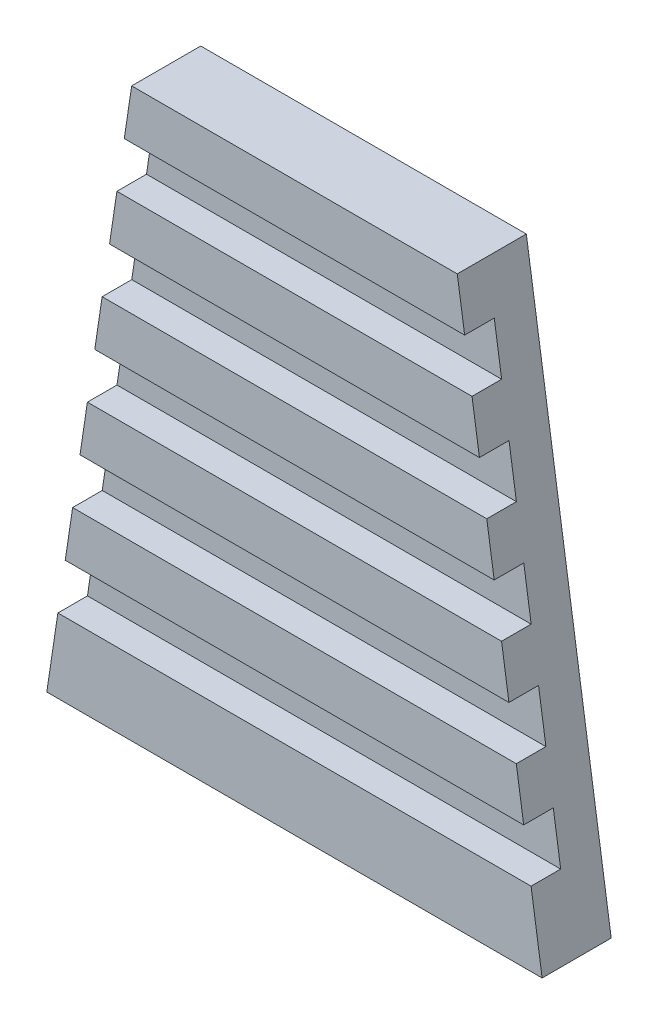
SolidWorks part; units mm, degrees
material "ABS"
ref_plane "Front Plane" through (0, 0, 0) normal (0, 0, 1) x (1, 0, 0)
ref_plane "Top Plane" through (0, 0, 0) normal (0, 1, 0) x (1, 0, 0)
ref_plane "Right Plane" through (0, 0, 0) normal (1, 0, 0) x (0, 0, -1)
sketch "Sketch1" plane through (0, 0, 0) normal (0, 0, 1) x (1, 0, 0)
  line L0 (-25.1, -28.75) -> (-16.5, 28.75)
  line L1 (-16.5, 28.75) -> (16.5, 28.75)
  line L2 (16.5, 28.75) -> (25.1, -28.75)
  line L3 (25.1, -28.75) -> (-25.1, -28.75)
  line L4 (0, -28.75) -> (0, 28.75) construction
  point P6 (0, 0)
  dimension "D1" = 57.5
  dimension "D2" = 33
  dimension "D3" = 50.2
extrude "Extrude1" add sketch "Sketch1" along normal blind 4
sketch "Sketch2" plane through (0, 0, 4) normal (0, 0, 1) x (1, 0, 0)
  line L4 (-17.2478, 23.75) -> (17.2478, 23.75)
  line L5 (-17.9957, 18.75) -> (17.9957, 18.75)
  line L6 (-18.7435, 13.75) -> (18.7435, 13.75)
  line L7 (-19.4913, 8.75) -> (19.4913, 8.75)
  line L8 (-25.1, -28.75) -> (25.1, -28.75)
  line L9 (25.1, -28.75) -> (16.5, 28.75)
  line L10 (16.5, 28.75) -> (-16.5, 28.75)
  line L11 (-16.5, 28.75) -> (-25.1, -28.75)
  line L12 (-25.1, -28.75) -> (25.1, -28.75)
  line L13 (25.1, -28.75) -> (23.9783, -21.25)
  line L14 (16.5, 28.75) -> (-16.5, 28.75)
  line L15 (-16.5, 28.75) -> (-17.2478, 23.75)
  line L16 (-20.2391, 3.75) -> (20.2391, 3.75)
  line L17 (-20.987, -1.25) -> (20.987, -1.25)
  line L18 (-21.7348, -6.25) -> (21.7348, -6.25)
  line L19 (-22.4826, -11.25) -> (22.4826, -11.25)
  line L20 (-23.2304, -16.25) -> (23.2304, -16.25)
  line L21 (-23.9783, -21.25) -> (23.9783, -21.25)
  line L23 (-17.9957, 18.75) -> (-18.7435, 13.75)
  line L24 (17.2478, 23.75) -> (16.5, 28.75)
  line L25 (18.7435, 13.75) -> (17.9957, 18.75)
  line L26 (20.2391, 3.75) -> (19.4913, 8.75)
  line L27 (21.7348, -6.25) -> (20.987, -1.25)
  line L28 (23.2304, -16.25) -> (22.4826, -11.25)
  line L29 (-23.9783, -21.25) -> (-25.1, -28.75)
  line L30 (-22.4826, -11.25) -> (-23.2304, -16.25)
  line L31 (-20.987, -1.25) -> (-21.7348, -6.25)
  line L32 (-19.4913, 8.75) -> (-20.2391, 3.75)
  dimension "D2" = 5
  dimension "D3" = 5
  dimension "D4" = 5
  dimension "D5" = 5
  dimension "D6" = 5
  dimension "D7" = 5
  dimension "D8" = 5
  dimension "D9" = 5
  dimension "D10" = 5
  dimension "D11" = 5
  dimension "D1" = 0
extrude "Extrude2" add sketch "Sketch2" along normal blind 3
